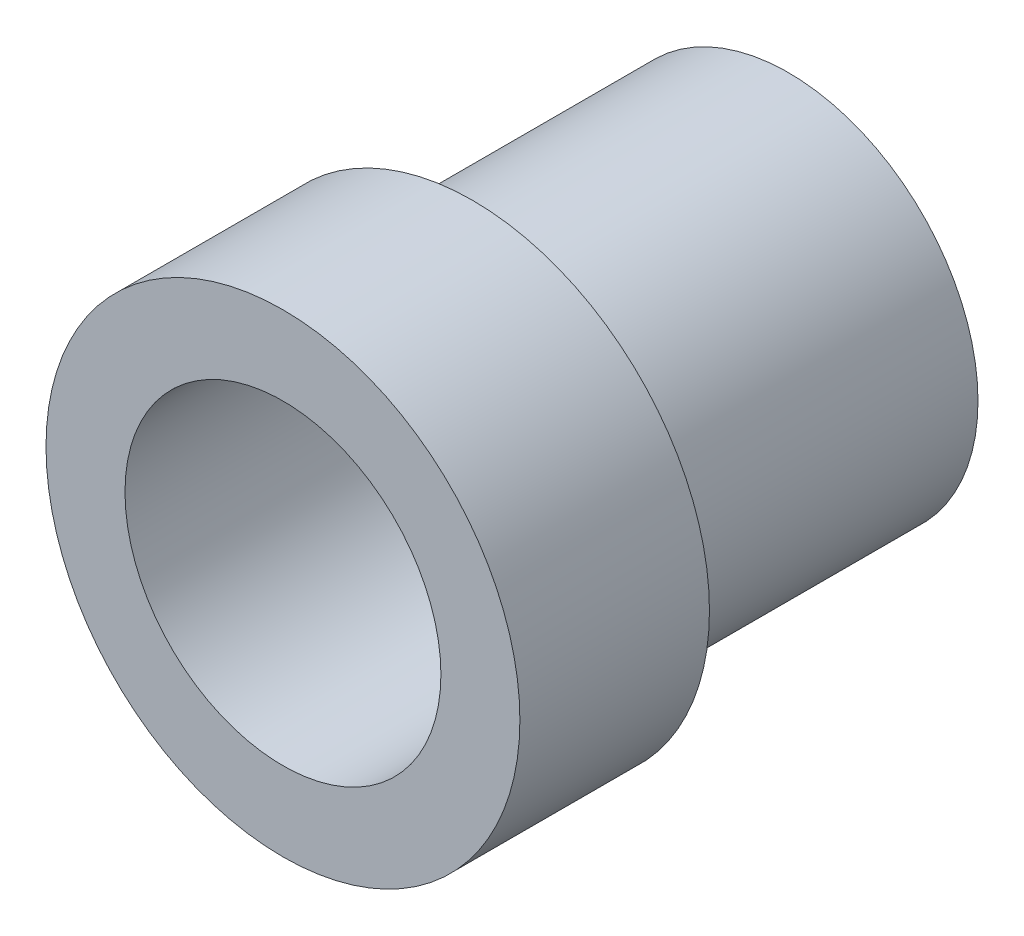
SolidWorks part; units mm, degrees
ref_plane "前视基准面" through (0, 0, 0) normal (0, 0, 1) x (1, 0, 0)
ref_plane "上视基准面" through (0, 0, 0) normal (0, 1, 0) x (1, 0, 0)
ref_plane "右视基准面" through (0, 0, 0) normal (1, 0, 0) x (0, 0, -1)
sketch "草图1" plane through (0, 0, 0) normal (0, 0, 1) x (1, 0, 0)
  circle A0 centre (0, 0) radius 6
  dimension "D1" = 12
extrude "凸台-拉伸1" add sketch "草图1" along normal blind 10
sketch "草图2" plane through (0, 0, 10) normal (0, 0, 1) x (1, 0, 0)
  circle A0 centre (0, 0) radius 7.5
  dimension "D1" = 15
extrude "凸台-拉伸2" add sketch "草图2" along normal blind 6
sketch "草图3" plane through (0, 0, 0) normal (0, 0, -1) x (-1, 0, 0)
  circle A0 centre (0, 0) radius 5
  dimension "D1" = 10
extrude "切除-拉伸1" cut sketch "草图3" against normal blind 24
